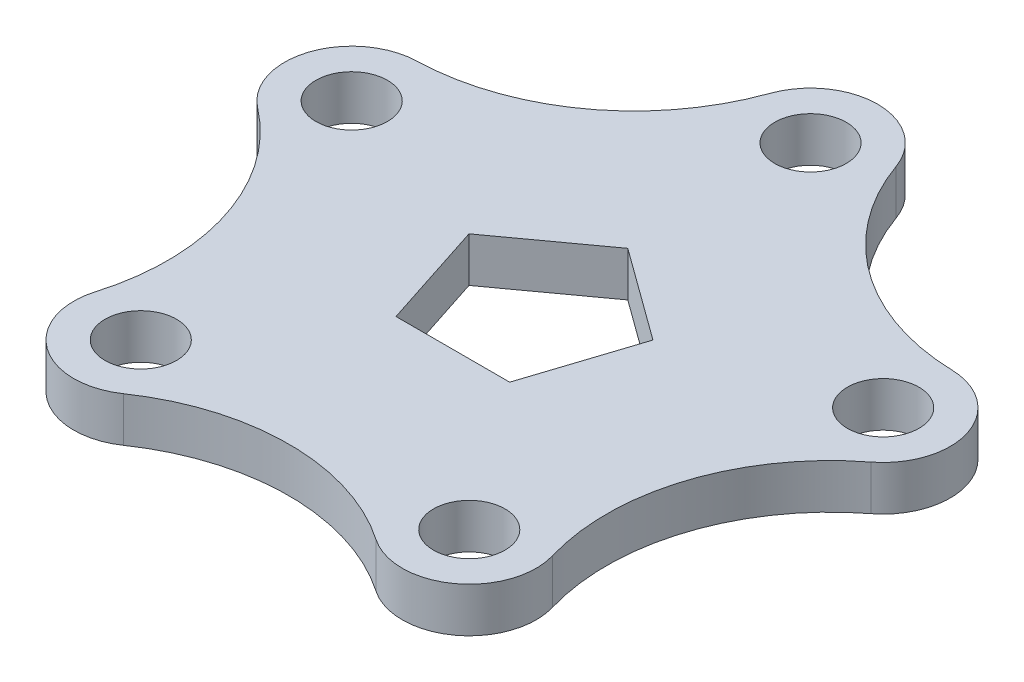
SolidWorks part; units mm, degrees
ref_plane "Front Plane" through (0, 0, 0) normal (0, 0, 1) x (1, 0, 0)
ref_plane "Top Plane" through (0, 0, 0) normal (0, 1, 0) x (1, 0, 0)
ref_plane "Right Plane" through (0, 0, 0) normal (1, 0, 0) x (0, 0, -1)
sketch "Sketch1" plane through (0, 0, 0) normal (0, 1, 0) x (1, 0, 0)
  line L1 (0, 21.6312) -> (-20.5725, 6.6844)
  line L2 (-20.5725, 6.6844) -> (-12.7145, -17.5)
  line L3 (-12.7145, -17.5) -> (12.7145, -17.5)
  line L4 (12.7145, -17.5) -> (20.5725, 6.6844)
  line L5 (20.5725, 6.6844) -> (0, 21.6312)
  line L6 (0, 62.5) -> (-59.441, 19.3136) construction
  line L7 (-59.441, 19.3136) -> (-36.7366, -50.5636) construction
  line L8 (-36.7366, -50.5636) -> (36.7366, -50.5636) construction
  line L9 (36.7366, -50.5636) -> (59.441, 19.3136) construction
  line L10 (59.441, 19.3136) -> (0, 62.5) construction
  circle A1 centre (0, 62.5) radius 8
  arc A2 (14.1321, 67.5282) -> (-14.1321, 67.5282) centre (0, 62.5) ccw
  circle A3 centre (59.441, 19.3136) radius 8
  arc A4 (68.5902, 7.4269) -> (59.856, 34.3078) centre (59.441, 19.3136) ccw
  circle A5 centre (36.7366, -50.5636) radius 8
  arc A6 (28.2589, -62.9381) -> (51.1252, -46.3248) centre (36.7366, -50.5636) ccw
  circle A7 centre (-36.7366, -50.5636) radius 8
  arc A8 (-51.1252, -46.3248) -> (-28.2589, -62.9381) centre (-36.7366, -50.5636) ccw
  circle A9 centre (-59.441, 19.3136) radius 8
  arc A10 (-59.856, 34.3078) -> (-68.5902, 7.4269) centre (-59.441, 19.3136) ccw
  circle A11 centre (0, 0) radius 17.5 construction
  circle A16 centre (0, 0) radius 50.5636 construction
  arc A18 (-59.856, 34.3078) -> (-14.1321, 67.5282) centre (-61.2393, 84.2887) ccw
  arc A19 (14.1321, 67.5282) -> (59.856, 34.3078) centre (61.2393, 84.2887) ccw
  arc A20 (68.5902, 7.4269) -> (51.1252, -46.3248) centre (99.0873, -32.1954) ccw
  arc A21 (28.2589, -62.9381) -> (-28.2589, -62.9381) centre (0, -104.1865) ccw
  arc A22 (-51.1252, -46.3248) -> (-68.5902, 7.4269) centre (-99.0873, -32.1954) ccw
  point P21 (0, 0)
  point P43 (0, 0)
  dimension "D2" = 16
  dimension "D3" = 30
  dimension "D5" = 35
  dimension "D6" = 100
  dimension "D4" = 5
  dimension "D7" = 5
extrude "Boss-Extrude2" add sketch "Sketch1" along normal mid plane 10
